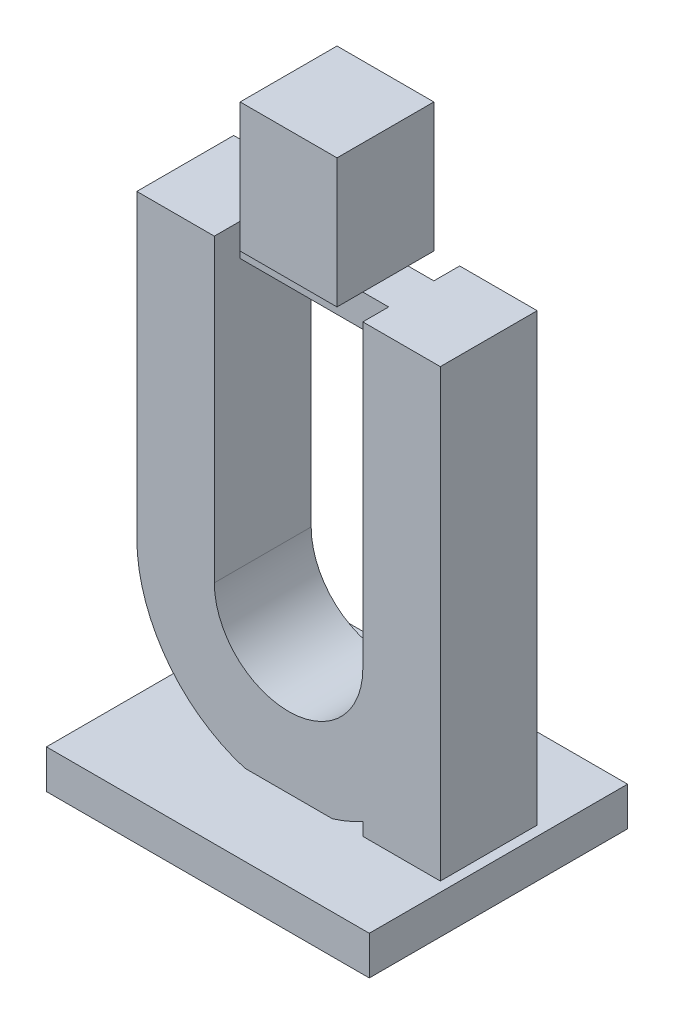
SolidWorks part; units mm, degrees
ref_plane "Vorne" through (0, 0, 0) normal (0, 0, 1) x (1, 0, 0)
ref_plane "Oben" through (0, 0, 0) normal (0, 1, 0) x (1, 0, 0)
ref_plane "Rechts" through (0, 0, 0) normal (1, 0, 0) x (0, 0, -1)
sketch "Skizze1" plane through (0, 0, 0) normal (0, 0, 1) x (1, 0, 0)
  line L0 (0, 0) -> (0, 70)
  line L1 (0, 70) -> (-12, 70)
  line L2 (-12, 70) -> (-12, 23.5)
  line L3 (-35, 23.5) -> (-35, 70)
  line L4 (-35, 70) -> (-47, 70)
  line L5 (-47, 70) -> (-47, 23.5)
  line L6 (-12, 3.0061) -> (-12, 0)
  line L7 (-12, 0) -> (0, 0)
  line L8 (58.1538, 0) -> (-95.8462, 0) construction
  line L9 (-23.5, 76.9865) -> (-23.5, -36.6289) construction
  arc A0 (-12, 23.5) -> (-35, 23.5) centre (-23.5, 23.5) cw
  arc A1 (-47, 23.5) -> (-12, 3.0061) centre (-23.5, 23.5) ccw
  point P17 (-23.5, 0)
  dimension "D1" = 70
  dimension "D2" = 12
  dimension "D3" = 12
  dimension "D4" = 47
extrude "Aufsatz-Linear austragen1" add sketch "Skizze1" along normal blind 15
sketch "Skizze2" plane through (0, 0, 0) normal (0, -1, 0) x (1, 0, 0)
  line L0 (-58.8495, 7.5) -> (10.5784, 7.5) construction
  line L1 (-23.5, 19.9428) -> (-23.5, -4.935) construction
  line L2 (-47, 0) -> (-12, 0) construction
  line L3 (-12, 15) -> (-47, 15) construction
  line L4 (-47, 15) -> (-47, 0) construction
  line L5 (0, 15) -> (0, 0) construction
  line L7 (-48.5, 27.5) -> (1.5, 27.5)
  line L8 (-48.5, 27.5) -> (-48.5, -12.5)
  line L9 (-48.5, -12.5) -> (1.5, -12.5)
  line L10 (1.5, 27.5) -> (1.5, -12.5)
  dimension "D1" = 50
  dimension "D2" = 40
extrude "Aufsatz-Linear austragen2" add sketch "Skizze2" along normal blind 5 and the other way blind 1
sketch "Skizze3" plane through (0, 70, 0) normal (0, 1, 0) x (1, 0, 0)
  line L0 (-61.5129, -7.5) -> (13.9706, -7.5) construction
  line L1 (-23.5, 17.1189) -> (-23.5, -26.8432) construction
  line L2 (-48.5, -27.5) -> (-48.5, 12.5) construction
  line L3 (1.5, 12.5) -> (1.5, -27.5) construction
  line L4 (1.5, -27.5) -> (-48.5, -27.5) construction
  line L5 (-48.5, 12.5) -> (1.5, 12.5) construction
  line L7 (-35, -15) -> (-35, 0) construction
  line L8 (-35, -4) -> (-12, -4)
  line L9 (-35, -4) -> (-35, -11)
  line L10 (-35, -11) -> (-12, -11)
  line L11 (-12, -4) -> (-12, -11)
  line L12 (-12, -15) -> (-12, 0) construction
  dimension "D1" = 7
extrude "Aufsatz-Linear austragen3" add sketch "Skizze3" against normal blind 5
sketch "Skizze4" plane through (0, 70, 0) normal (0, 1, 0) x (1, 0, 0)
  line L0 (-58.4103, -7.5) -> (9.2933, -7.5) construction
  line L1 (-23.5, 11.7942) -> (-23.5, -25.1868) construction
  line L2 (1.5, -27.5) -> (-48.5, -27.5) construction
  line L3 (-48.5, 12.5) -> (1.5, 12.5) construction
  line L4 (-48.5, -27.5) -> (-48.5, 12.5) construction
  line L5 (1.5, 12.5) -> (1.5, -27.5) construction
  line L6 (-12, 0) -> (-35, 0) construction
  line L7 (-31, 0) -> (-16, 0)
  line L8 (-31, 0) -> (-31, -15)
  line L9 (-31, -15) -> (-16, -15)
  line L10 (-16, 0) -> (-16, -15)
  line L11 (-35, -15) -> (-12, -15) construction
  dimension "D1" = 15
extrude "Aufsatz-Linear austragen4" add sketch "Skizze4" along normal blind 20
